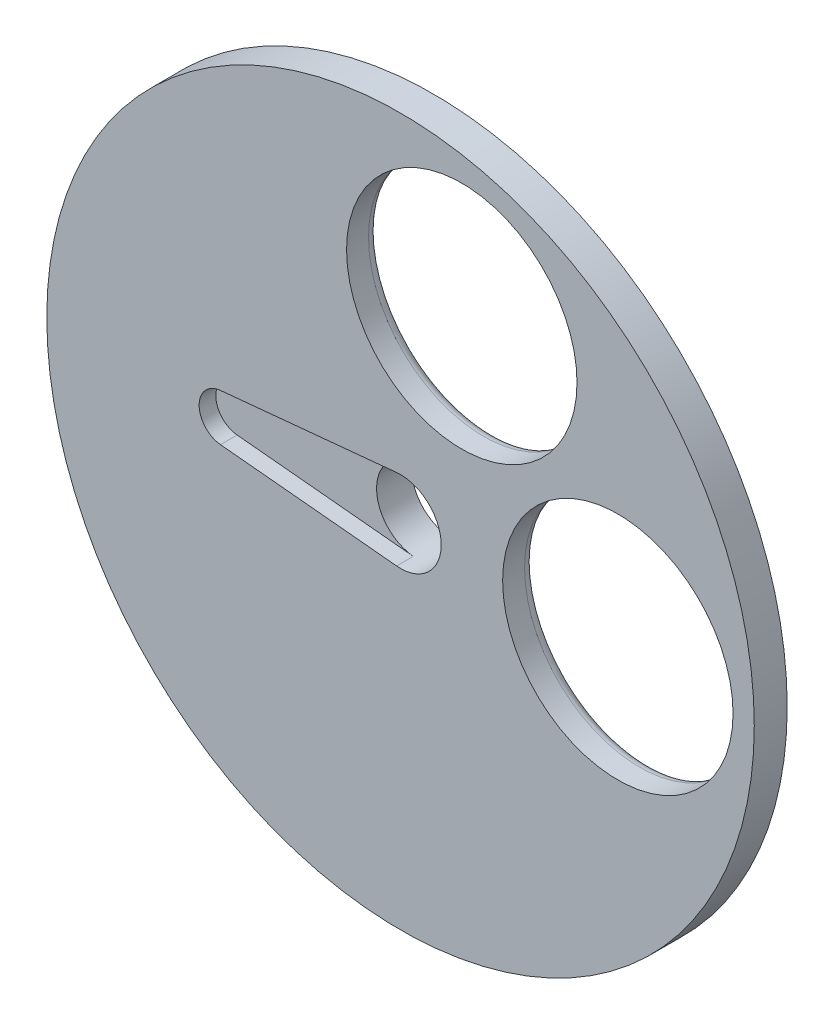
SolidWorks part; units mm, degrees
ref_plane "前视基准面" through (0, 0, 0) normal (0, 0, 1) x (1, 0, 0)
ref_plane "上视基准面" through (0, 0, 0) normal (0, 1, 0) x (1, 0, 0)
ref_plane "右视基准面" through (0, 0, 0) normal (1, 0, 0) x (0, 0, -1)
sketch "草图1" plane through (0, 0, 0) normal (0, 0, 1) x (1, 0, 0)
  line L2 (5.5819, 19) -> (0, 0) construction
  line L3 (0, 0) -> (32.2367, 0) construction
  line L4 (-0.3555, 3.6879) -> (-16.4113, 2.1401)
  line L5 (-16.4113, -2.1401) -> (-0.3555, -3.6879)
  line L6 (-0.3555, 3.6879) -> (-16.4113, 2.1401)
  line L7 (-16.4113, -2.1401) -> (-0.3555, -3.6879)
  circle A2 centre (0, 0) radius 32.2367
  circle A3 centre (0, 0) radius 19.803 construction
  arc A4 (-0.3555, -3.6879) -> (-0.3555, 3.6879) centre (0, 0) ccw
  arc A5 (-16.4113, 2.1401) -> (-16.4113, -2.1401) centre (-16.205, 0) ccw
  arc A6 (-0.3555, -3.6879) -> (-0.3555, 3.6879) centre (0, 0) ccw
  arc A7 (-16.4113, 2.1401) -> (-16.4113, -2.1401) centre (-16.205, 0) ccw
  circle A8 centre (5.5819, 19) radius 10.5
  circle A9 centre (19.803, 0) radius 10.5
  dimension "D1" = 0.3
extrude "凸台-拉伸1" add sketch "草图1" against normal up to surface (1.52 mm away)
sketch "草图2" plane through (0, 0, -1.52) normal (0, 0, -1) x (-1, 0, 0)
  circle A0 centre (-5.5819, 19) radius 10.5 construction
  circle A1 centre (0, 0) radius 32.2367
  circle A2 centre (0, 0) radius 32.2367
  circle A3 centre (-19.803, 0) radius 10.5 construction
  circle A4 centre (-5.5819, 19) radius 10.5
  circle A5 centre (-19.803, 0) radius 10.5
  circle A6 centre (0, 0) radius 3.705
  dimension "D1" = 0
extrude "凸台-拉伸2" add sketch "草图2" along normal offset from surface (1.48 mm away) 3 up to face at (-7.8542, 0, 0)
fillet "圆角1" radius 1 2 edges at (16.0819, 19, -3) (30.303, 0, -3)
sketch "草图3" plane through (0, 0, -3) normal (0, 0, -1) x (-1, 0, 0)
  circle A0 centre (0, 0) radius 3.705 construction
  circle A1 centre (0, 0) radius 3.705
extrude "拉伸-薄壁1" add sketch "草图3" along normal up to surface (1.7 mm away) thin
